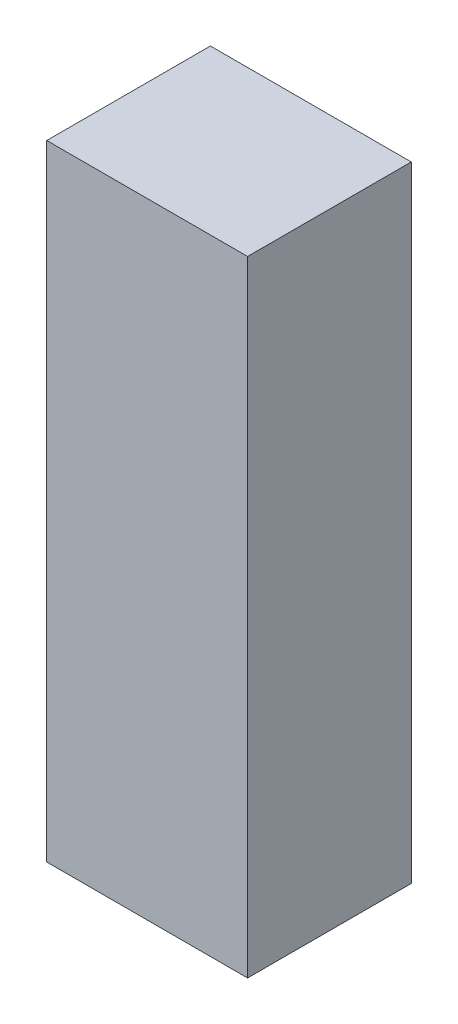
SolidWorks part; units mm, degrees
ref_plane "Front Plane" through (0, 0, 0) normal (0, 0, 1) x (1, 0, 0)
ref_plane "Top Plane" through (0, 0, 0) normal (0, 1, 0) x (1, 0, 0)
ref_plane "Right Plane" through (0, 0, 0) normal (1, 0, 0) x (0, 0, -1)
sketch "Sketch1" plane through (0, 0, 0) normal (0, 1, 0) x (1, 0, 0)
  line L1 (-342.9, -279.4) -> (342.9, -279.4)
  line L2 (-342.9, -279.4) -> (-342.9, 279.4)
  line L3 (-342.9, 279.4) -> (342.9, 279.4)
  line L4 (342.9, -279.4) -> (342.9, 279.4)
  line L5 (-342.9, -279.4) -> (342.9, 279.4) construction
  line L6 (-342.9, 279.4) -> (342.9, -279.4) construction
  point P0 (0, 0)
  dimension "D1" = 558.8
  dimension "D2" = 685.8
extrude "Boss-Extrude1" add sketch "Sketch1" along normal blind 2133.6
shell "Shell1" thickness 3.175
